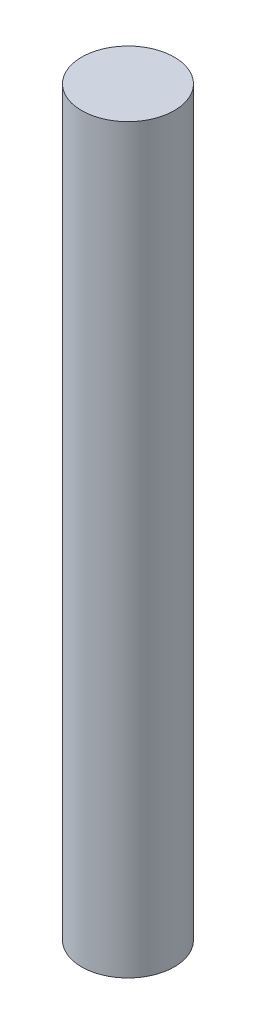
SolidWorks part; units mm, degrees
ref_plane "Front Plane" through (0, 0, 0) normal (0, 0, 1) x (1, 0, 0)
ref_plane "Top Plane" through (0, 0, 0) normal (0, 1, 0) x (1, 0, 0)
ref_plane "Right Plane" through (0, 0, 0) normal (1, 0, 0) x (0, 0, -1)
sketch "Sketch1" plane through (0, 0, 0) normal (0, 1, 0) x (1, 0, 0)
  circle A0 centre (0, 0) radius 3.175
  dimension "D1" = 6.35
extrude "Boss-Extrude1" add sketch "Sketch1" along normal blind 50.8 contours A0
